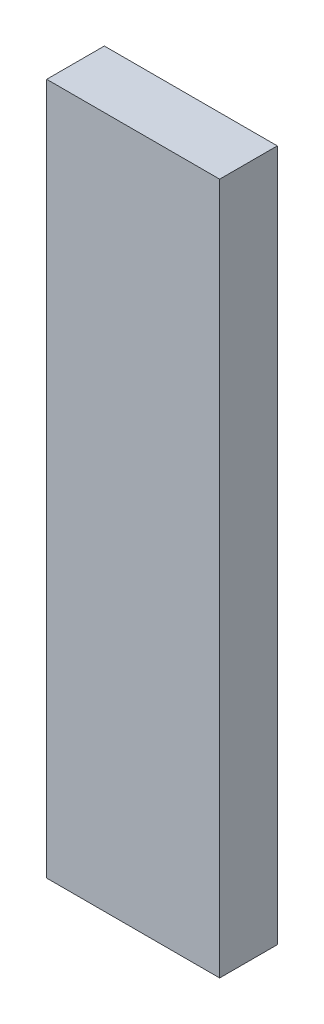
SolidWorks part; units mm, degrees
ref_plane "Спереди" through (0, 0, 0) normal (0, 0, 1) x (1, 0, 0)
ref_plane "Сверху" through (0, 0, 0) normal (0, 1, 0) x (1, 0, 0)
ref_plane "Справа" through (0, 0, 0) normal (1, 0, 0) x (0, 0, -1)
sketch "Эскиз1" plane through (0, 0, 0) normal (0, 0, 1) x (1, 0, 0)
  line L1 (-0.45, -1.8) -> (0.45, -1.8)
  line L2 (-0.45, -1.8) -> (-0.45, 1.8)
  line L3 (-0.45, 1.8) -> (0.45, 1.8)
  line L4 (0.45, -1.8) -> (0.45, 1.8)
  line L5 (-0.45, -1.8) -> (0.45, 1.8) construction
  line L6 (-0.45, 1.8) -> (0.45, -1.8) construction
  point P0 (0, 0)
  dimension "D1" = 0.9
  dimension "D2" = 3.6
extrude "Бобышка-Вытянуть1" add sketch "Эскиз1" along normal blind 0.3
